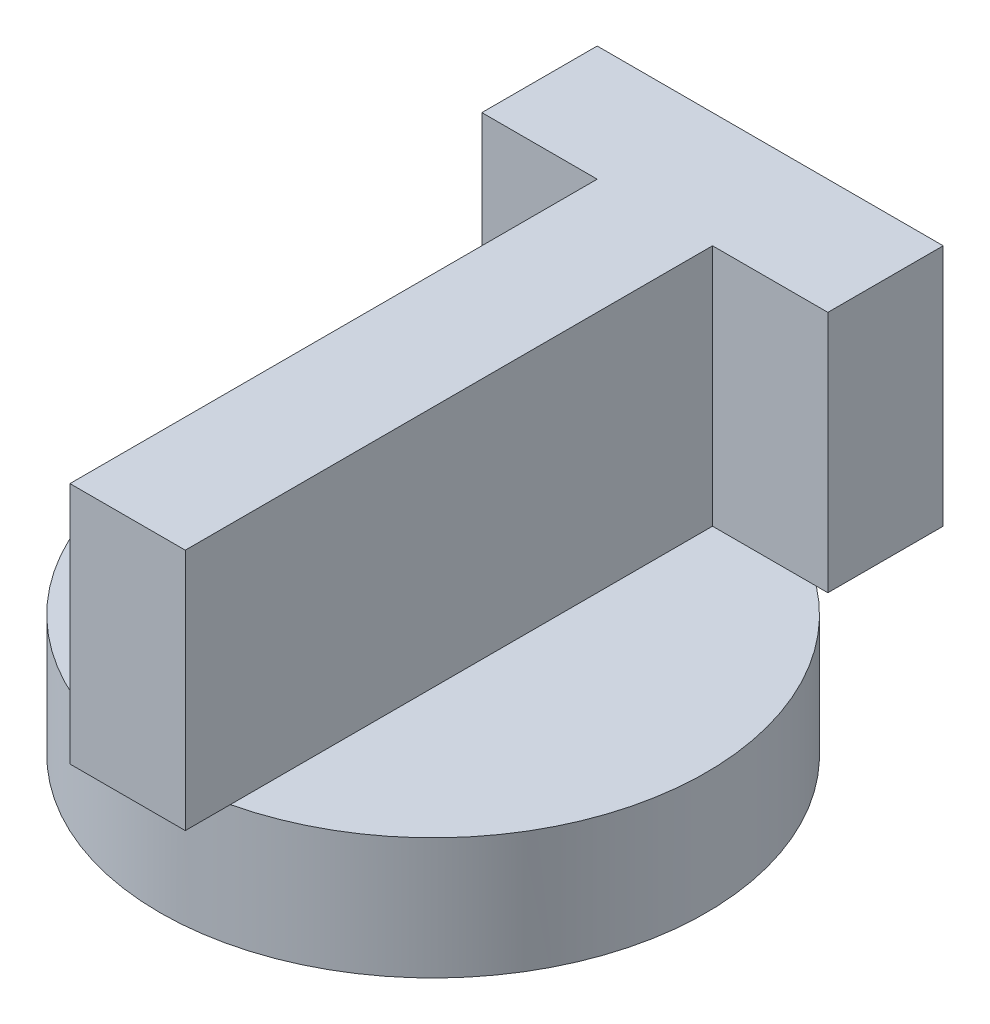
SolidWorks part; units mm, degrees
ref_plane "Front Plane" through (0, 0, 0) normal (0, 0, 1) x (1, 0, 0)
ref_plane "Top Plane" through (0, 0, 0) normal (0, 1, 0) x (1, 0, 0)
ref_plane "Right Plane" through (0, 0, 0) normal (1, 0, 0) x (0, 0, -1)
sketch "Sketch1" plane through (0, 0, 0) normal (0, 1, 0) x (1, 0, 0)
  circle A0 centre (0, 0) radius 22.5
  dimension "D1" = 45
extrude "Boss-Extrude1" add sketch "Sketch1" along normal blind 10
sketch "Sketch2" plane through (0, 10, 0) normal (0, 1, 0) x (1, 0, 0)
  text T0 "<b>T</b>" font "Century Gothic" height in points 200
extrude "Boss-Extrude2" add sketch "Sketch2" along normal blind 20
sketch "Sketch3" plane through (0, 0, 0) normal (0, -1, 0) x (1, 0, 0)
  line L0 (14.5514, 2.7786) -> (0, 30)
  line L1 (0, 30) -> (-14.5514, 2.7786)
  circle A0 centre (0, -5) radius 16.5
  circle A2 centre (0, 0) radius 22.5 construction
  circle A4 centre (0, 0) radius 21.5
  circle A5 centre (0, 0) radius 21.5
  dimension "D1" = 33
  dimension "D2" = 35
  dimension "D3" = 5
  dimension "D4" = 1
extrude "Cut-Extrude2" cut sketch "Sketch3" against normal blind 5 contours L0 A5 L1 A0 | A0
